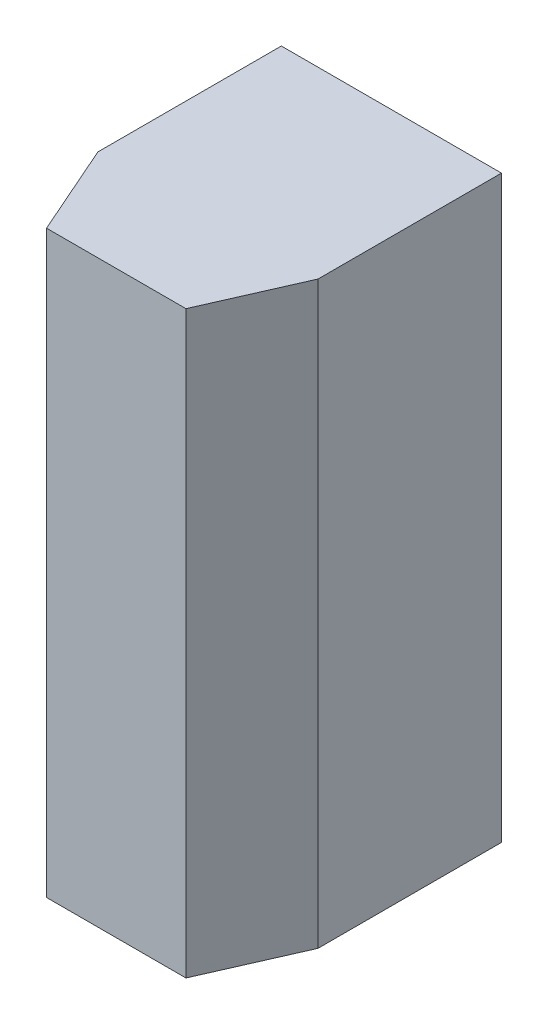
SolidWorks part; units mm, degrees
ref_plane "Front Plane" through (0, 0, 0) normal (0, 0, 1) x (1, 0, 0)
ref_plane "Top Plane" through (0, 0, 0) normal (0, 1, 0) x (1, 0, 0)
ref_plane "Right Plane" through (0, 0, 0) normal (1, 0, 0) x (0, 0, -1)
sketch "Sketch1" plane through (0, 0, 0) normal (0, 0, 1) x (1, 0, 0)
  line L1 (0, 0) -> (7.62, 0)
  line L2 (0, 0) -> (0, 20.066)
  line L3 (0, 20.066) -> (7.62, 20.066)
  line L4 (7.62, 0) -> (7.62, 20.066)
  dimension "D1" = 20.066
  dimension "D2" = 7.62
extrude "Boss-Extrude1" add sketch "Sketch1" along normal blind 6.35
sketch "Sketch4" plane through (0, 0, 0) normal (0, -1, 0) x (1, 0, 0)
  line L0 (0, 6.35) -> (1.397, 9.525)
  line L1 (1.397, 9.525) -> (6.223, 9.525)
  line L2 (6.223, 9.525) -> (7.62, 6.35)
  line L3 (7.62, 6.35) -> (0, 6.35)
  line L4 (3.81, 9.525) -> (3.81, 6.35) construction
  dimension "D1" = 3.175
  dimension "D2" = 4.826
extrude "Boss-Extrude2" add sketch "Sketch4" against normal up to surface (20.066 mm away) up to face at (3.81, 20.066, 3.175)
